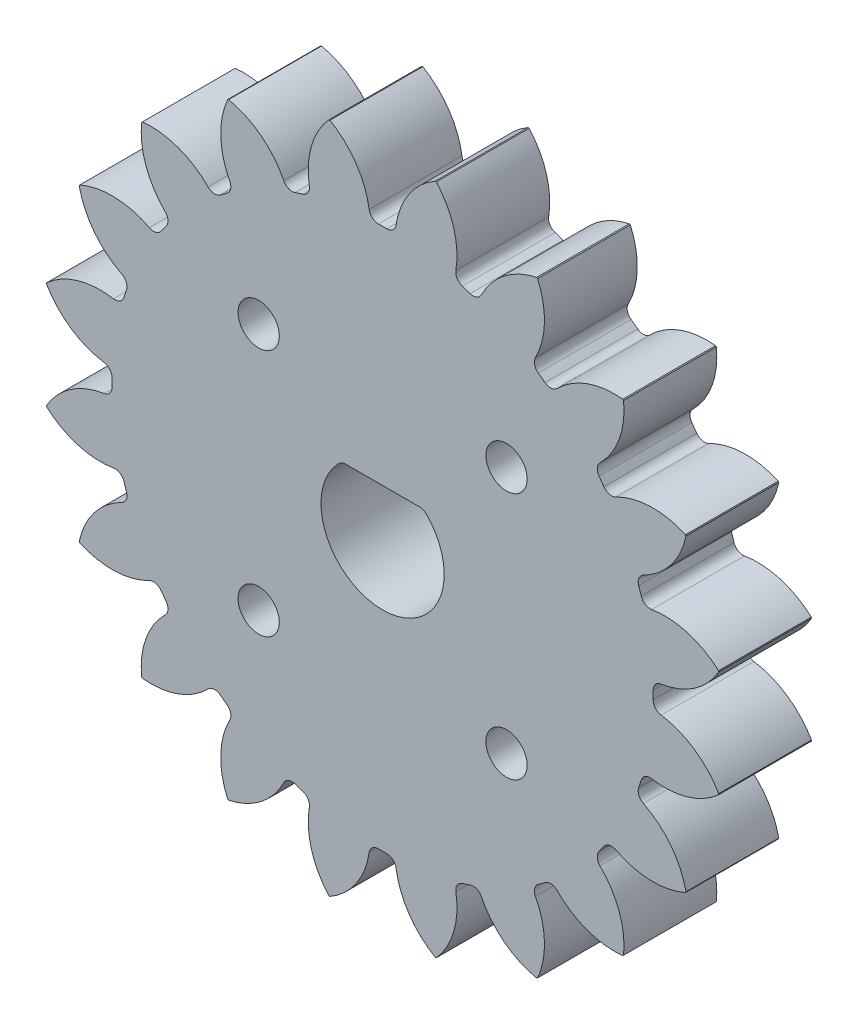
SolidWorks part; units mm, degrees
ref_plane "Front Plane" through (0, 0, 0) normal (0, 0, 1) x (1, 0, 0)
ref_plane "Top Plane" through (0, 0, 0) normal (0, 1, 0) x (1, 0, 0)
ref_plane "Right Plane" through (0, 0, 0) normal (1, 0, 0) x (0, 0, -1)
sketch "Sketch1" plane through (0, 0, 0) normal (0, 0, 1) x (1, 0, 0)
  circle A0 centre (0, 0) radius 30
  circle A1 centre (0, 0) radius 33
  dimension "D1" = 60
  dimension "D2" = 66
extrude "Boss-Extrude1" add sketch "Sketch1" along normal blind 9 contours A1 A0
sketch "Sketch2" plane through (0, 0, 9) normal (0, 0, 1) x (1, 0, 0)
  line L0 (0, 33) -> (0, 0) construction
  line L1 (0, 0) -> (10.1976, 31.3849) construction
  line L2 (0, 0) -> (5.1623, 32.5937) construction
  line L3 (-1.2265, 26.2213) -> (0, 0) construction
  line L4 (-2.3538, 29.9075) -> (2.3538, 29.9075) construction
  line L5 (2.3538, 29.9075) -> (7.0034, 29.1711) construction
  line L6 (-3.2591, 32.8387) -> (0, 23.8843) construction
  circle A0 centre (0, 0) radius 27 construction
  circle A2 centre (0, 0) radius 33 construction
  arc A3 (-5.1104, 32.6019) -> (-1.2265, 26.2213) centre (-9.0076, 25.8574) cw
  circle A4 centre (0, 0) radius 33 construction
  arc A5 (5.1104, 32.6019) -> (1.2265, 26.2213) centre (9.0076, 25.8574) ccw
  circle A6 centre (0, 0) radius 30 construction
  arc A7 (1.2265, 26.2213) -> (-1.2265, 26.2213) centre (0, 0) ccw
  circle M1 centre (0, 0) radius 33
  dimension "D1" = 18
  dimension "D2" = 6
  dimension "D4" = 20
  dimension "D3" = 0.75
extrude "Cut-Extrude1" cut sketch "Sketch2" against normal through all both and the other way through all contours A7 A5 A3 M1
fillet "Fillet1" radius 0.9 2 edges at (1.2265, 26.2213, 4.5) (-1.2265, 26.2213, 4.5)
pattern_circular "CirPattern3" count 20 over 360 about axis through (0, 0, 0) along (0, 0, 1) of "Fillet1", "Cut-Extrude1"
sketch "Sketch3" plane through (0, 0, 9) normal (0, 0, 1) x (1, 0, 0)
  line L1 (-3.9592, 4.475) -> (3.9592, 4.475)
  circle A1 centre (0, 0) radius 5.975
  point P2 (0, 5.975)
  dimension "D1" = 11.95
  dimension "D2" = 1.5
sketch "Sketch4" plane through (0, 0, 9) normal (0, 0, 1) x (1, 0, 0)
  line L0 (0, 0) -> (26.25, 0) construction
  line L1 (0, 0) -> (0, 26.25) construction
  line L2 (18.5616, 18.5616) -> (0, 0) construction
  circle A0 centre (0, 0) radius 26.25
  circle A1 centre (12.0208, 12.0208) radius 2
  circle A2 centre (-12.0208, 12.0208) radius 2
  circle A3 centre (-12.0208, -12.0208) radius 2
  circle A4 centre (12.0208, -12.0208) radius 2
  point P4 (18.5616, 18.5616)
  dimension "D3" = 4
  dimension "D1" = 45
  dimension "D2" = 17
extrude "Cut-Extrude4" cut sketch "Sketch4" against normal through all contours A2 | A1 | A4 | A3
extrude "Cut-Extrude5" cut sketch "Sketch3" against normal through all contours L1 A1
fillet "Fillet2" radius 1 2 edges at (-3.9592, 4.475, 4.5) (3.9592, 4.475, 4.5)
equation "\"Module\"= 3mm"
equation "\"No. Teeth\"= 20"
equation "\"Contact Angle\"= 20"
equation "\"D1@Sketch1\"=\"Module\" * \"No. Teeth\""
equation "\"D2@Sketch1\"=(\"No. Teeth\" + 2) * \"Module\""
equation "\"D1@Sketch2\"=360/\"No. Teeth\""
equation "\"D2@Sketch2\"=2*\"Module\""
equation "\"D4@Sketch2\"=\"Contact Angle\""
equation "\"D1@Fillet1\"=0.3 * \"Module\""
equation "\"D1@CirPattern3\"=\"No. Teeth\""
